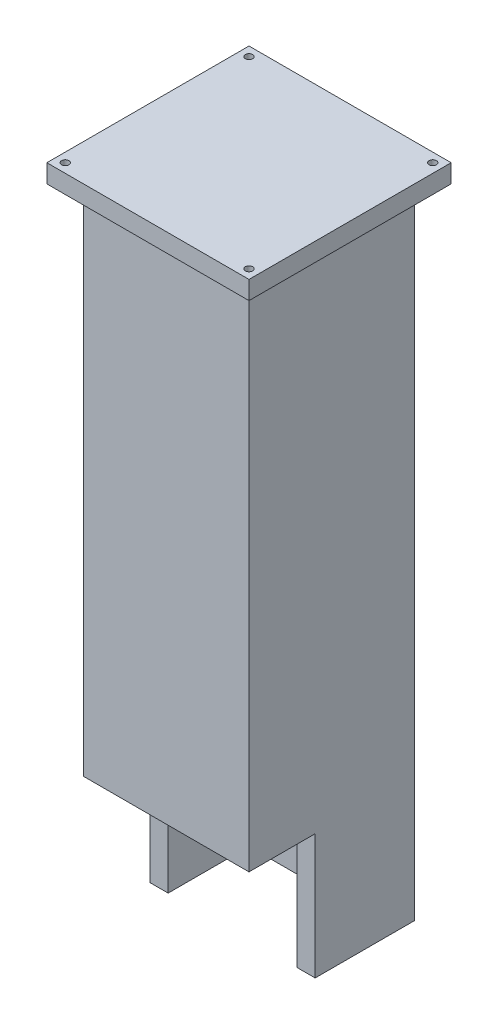
SolidWorks part; units mm, degrees
ref_plane "Alzado" through (0, 0, 0) normal (0, 0, 1) x (1, 0, 0)
ref_plane "Planta" through (0, 0, 0) normal (0, 1, 0) x (1, 0, 0)
ref_plane "Vista lateral" through (0, 0, 0) normal (1, 0, 0) x (0, 0, -1)
sketch "Croquis1" plane through (0, 0, 0) normal (0, 1, 0) x (1, 0, 0)
  line L1 (-22.5, -22.5) -> (22.5, -22.5)
  line L2 (-22.5, -22.5) -> (-22.5, 22.5)
  line L3 (-22.5, 22.5) -> (22.5, 22.5)
  line L4 (22.5, -22.5) -> (22.5, 22.5)
  line L5 (-22.5, -22.5) -> (22.5, 22.5) construction
  line L6 (-22.5, 22.5) -> (22.5, -22.5) construction
  point P0 (0, 0)
  dimension "D1" = 45
  dimension "D2" = 45
extrude "Saliente-Extruir1" add sketch "Croquis1" along normal blind 300
sketch "Croquis4" plane through (-22.5, 0, 0) normal (-1, 0, 0) x (0, 0, 1)
  line L1 (22.5, 300) -> (22.5, 0) construction
  line L3 (55, 0) -> (-55, 0) construction
  line L5 (4.5, 0) -> (4.5, 34)
  line L6 (4.5, 34) -> (22.5, 34)
  line L8 (22.5, 34) -> (22.5, 0)
  line L9 (22.5, 0) -> (4.5, 0)
  dimension "D4" = 34
extrude "Cortar-Extruir2" cut sketch "Croquis4" against normal through all
sketch "Croquis7" plane through (0, 0, 22.5) normal (0, 0, 1) x (1, 0, 0)
  line L0 (0, -24.75) -> (0, 24.75) construction
  line L1 (-22.5, 246.3879) -> (22.5, 246.3879)
  line L2 (-22.5, 246.3879) -> (-22.5, 273.6121)
  line L3 (-22.5, 273.6121) -> (22.5, 273.6121)
  line L4 (22.5, 246.3879) -> (22.5, 273.6121)
  line L5 (-22.5, 246.3879) -> (22.5, 273.6121) construction
  line L6 (-22.5, 273.6121) -> (22.5, 246.3879) construction
  line L7 (22.5, 300) -> (22.5, 34) construction
  point P0 (0, 260)
  dimension "D1" = 260
sketch "Croquis8" plane through (0, 300, 0) normal (0, 1, 0) x (1, 0, 0)
  line L0 (22.5, -22.5) -> (22.5, 22.5) construction
  line L1 (-17.5, -17.5) -> (17.5, -17.5)
  line L2 (-17.5, -17.5) -> (-17.5, 17.5)
  line L3 (-17.5, 17.5) -> (17.5, 17.5)
  line L4 (17.5, -17.5) -> (17.5, 17.5)
  line L5 (-17.5, -17.5) -> (17.5, 17.5) construction
  line L6 (-17.5, 17.5) -> (17.5, -17.5) construction
  line L7 (22.5, 22.5) -> (-22.5, 22.5) construction
  point P0 (0, 0)
  dimension "D1" = 5
  dimension "D2" = 5
extrude "Cortar-Extruir3" cut sketch "Croquis8" against normal through all contours L3 L4 L1 L2
sketch "Croquis9" plane through (0, 0, -22.5) normal (0, 0, -1) x (-1, 0, 0)
  line L0 (22.5, 273.6121) -> (-22.5, 246.3879) construction
  line L1 (-17.5, 249.4128) -> (17.5, 249.4128)
  line L2 (-17.5, 249.4128) -> (-17.5, 270.5872)
  line L3 (-17.5, 270.5872) -> (17.5, 270.5872)
  line L4 (17.5, 249.4128) -> (17.5, 270.5872)
  line L5 (-17.5, 249.4128) -> (17.5, 270.5872) construction
  line L6 (-17.5, 270.5872) -> (17.5, 249.4128) construction
  line L7 (22.5, 246.3879) -> (22.5, 273.6121) construction
  point P0 (0, 260)
  point P10 (22.5, 260)
  dimension "D1" = 5
extrude "Cortar-Extruir4" cut sketch "Croquis9" against normal blind 10 contours L4 L3 L2 L1
sketch "Croquis10" plane through (0, 0, 22.5) normal (0, 0, 1) x (1, 0, 0)
  circle A0 centre (0, 260) radius 1
  dimension "D1" = 2
extrude "Cortar-Extruir5" cut sketch "Croquis10" against normal blind 10
sketch "Croquis11" plane through (0, 0, 22.5) normal (0, 0, 1) x (1, 0, 0)
  line L0 (22.5, 300) -> (22.5, 34) construction
  line L1 (-22.5, 300) -> (22.5, 300)
  line L2 (-22.5, 300) -> (-22.5, 273.6121)
  line L3 (-22.5, 273.6121) -> (22.5, 273.6121)
  line L4 (22.5, 300) -> (22.5, 273.6121)
  line L5 (-22.5, 273.6121) -> (22.5, 273.6121) construction
  dimension "D1" = 0
extrude "Cortar-Extruir6" cut sketch "Croquis11" against normal through all
sketch "Croquis12" plane through (0, 0, 22.5) normal (0, 0, 1) x (1, 0, 0)
  line L0 (-22.5, 267.3717) -> (22.5, 246.3879)
  line L1 (-22.5, 246.3879) -> (-22.5, 273.6121) construction
  line L2 (-22.5, 246.3879) -> (22.5, 246.3879) construction
  dimension "D1" = 25
sketch "Croquis13" plane through (0, 0, 0) normal (1, 0, 0) x (0, 0, -1)
  line L0 (-22.5, 273.6121) -> (-22.5, 34) construction
  line L1 (-22.5, 173.6121) -> (22.5, 173.6121)
  line L10 (-22.5, 173.6121) -> (-22.5, 273.6121)
  line L11 (-22.5, 273.6121) -> (22.5, 273.6121)
  line L12 (22.5, 173.6121) -> (22.5, 273.6121)
  dimension "D1" = 100
extrude "Cortar-Extruir9" cut sketch "Croquis13" against normal through all both and the other way through all
sketch "Croquis14" plane through (0, 173.6121, 0) normal (0, 1, 0) x (1, 0, 0)
  line L1 (-27.5, -27.5) -> (27.5, -27.5)
  line L2 (-27.5, -27.5) -> (-27.5, 27.5)
  line L3 (-27.5, 27.5) -> (27.5, 27.5)
  line L4 (27.5, -27.5) -> (27.5, 27.5)
  line L5 (-27.5, -27.5) -> (27.5, 27.5) construction
  line L6 (-27.5, 27.5) -> (27.5, -27.5) construction
  circle A0 centre (-25, 25) radius 1
  circle A1 centre (25, -25) radius 1
  circle A2 centre (25, 25) radius 1
  circle A3 centre (-25, -25) radius 1
  point P0 (0, 0)
  dimension "D7" = 2
  dimension "D1" = 27.5
  dimension "D2" = 27.5
  dimension "D3" = 2.5
  dimension "D4" = 2.5
  dimension "D5" = 2.5
  dimension "D6" = 2.5
extrude "Saliente-Extruir3" add sketch "Croquis14" along normal blind 5
